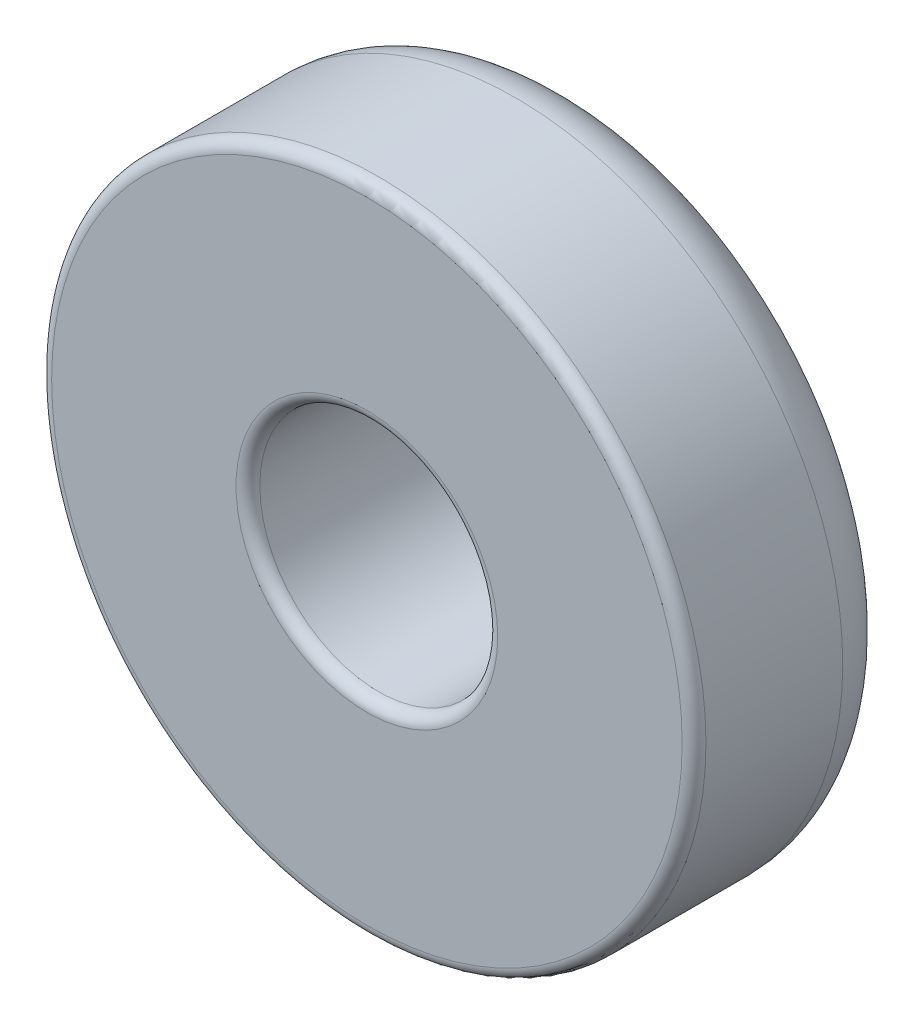
SolidWorks part; units mm, degrees
ref_plane "Ön Düzlem" through (0, 0, 0) normal (0, 0, 1) x (1, 0, 0)
ref_plane "Üst Düzlem" through (0, 0, 0) normal (0, 1, 0) x (1, 0, 0)
ref_plane "Sağ Düzlem" through (0, 0, 0) normal (1, 0, 0) x (0, 0, -1)
sketch "Sketch2" plane through (0, 0, 0) normal (0, 0, 1) x (1, 0, 0)
  circle A0 centre (0, 0) radius 1
  dimension "D1" = 2
extrude "Extrude-Thin1" add sketch "Sketch2" along normal blind 1.75 thin
fillet "Fillet1" radius 0.5 1 edges at (2.75, 0, 0)
fillet "Fillet2" radius 0.1 3 edges at (1, 0, 1.75) (2.75, 0, 1.75) (1, 0, 0)
